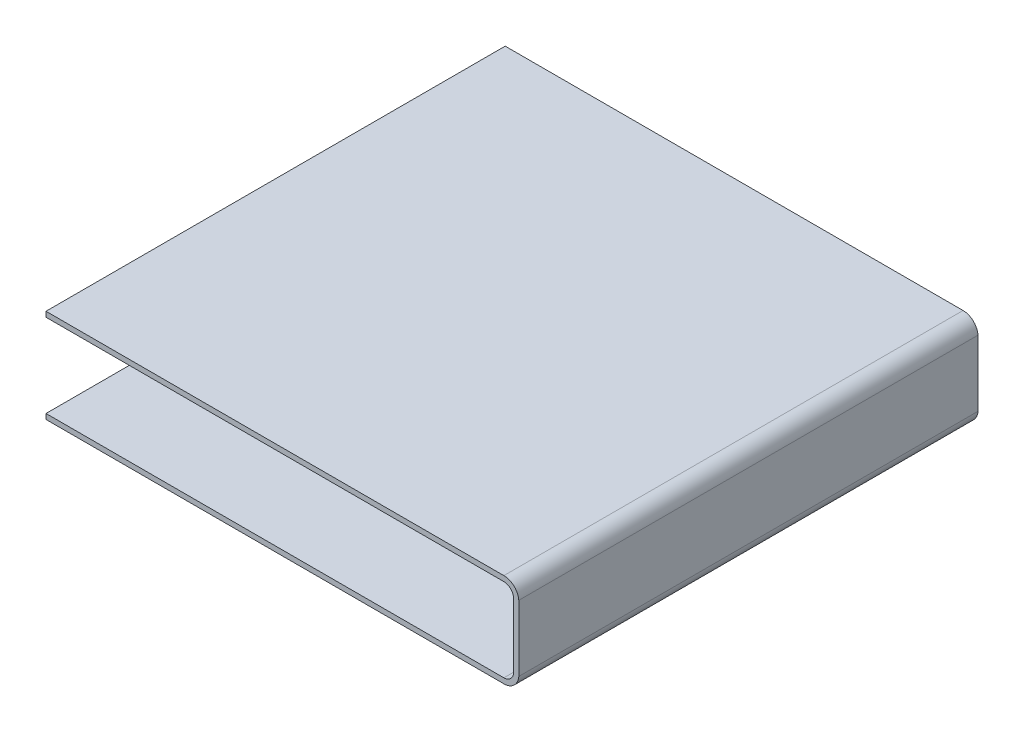
SolidWorks part; units mm, degrees
ref_plane "Front Plane" through (0, 0, 0) normal (0, 0, 1) x (1, 0, 0)
ref_plane "Top Plane" through (0, 0, 0) normal (0, 1, 0) x (1, 0, 0)
ref_plane "Right Plane" through (0, 0, 0) normal (1, 0, 0) x (0, 0, -1)
sketch "Sketch1" plane through (0, 0, 0) normal (0, 0, 1) x (1, 0, 0)
  line L0 (-1262.2956, 1976) -> (8389.7044, 1976)
  line L3 (-1262.2956, 0) -> (8389.7044, 0)
  line L4 (8704.507, 1682.8027) -> (8704.507, 293.1973)
  arc A0 (8389.7044, 0) -> (8704.507, 293.1973) centre (8389.7044, 315.5987) ccw
  arc A1 (8389.7044, 1976) -> (8704.507, 1682.8027) centre (8389.7044, 1660.4013) cw
  point P6 (9892.6888, 988)
extrude "Extrude-Thin3" add sketch "Sketch1" along normal blind 9680 thin
sketch "Sketch3" plane through (0, 0, 0) normal (0, 1, 0) x (1, 0, 0)
  line L0 (955.2644, -1000) -> (8389.7044, -1000) construction
  line L1 (8389.7044, -8680) -> (955.2644, -8680)
  line L2 (8389.7044, -9680) -> (8389.7044, 0) construction
  line L3 (955.2644, -8680) -> (8389.7044, -8680) construction
  line L5 (0, -1706.2625) -> (0, -7973.7375)
  line L8 (8389.7044, -1000) -> (955.2644, -1000)
  arc A0 (955.2644, -1000) -> (0, -1706.2625) centre (955.2644, -1999.1588) ccw
  arc A1 (955.2644, -8680) -> (0, -7973.7375) centre (955.2644, -7680.8412) cw
  point P11 (0, -1706.2625)
